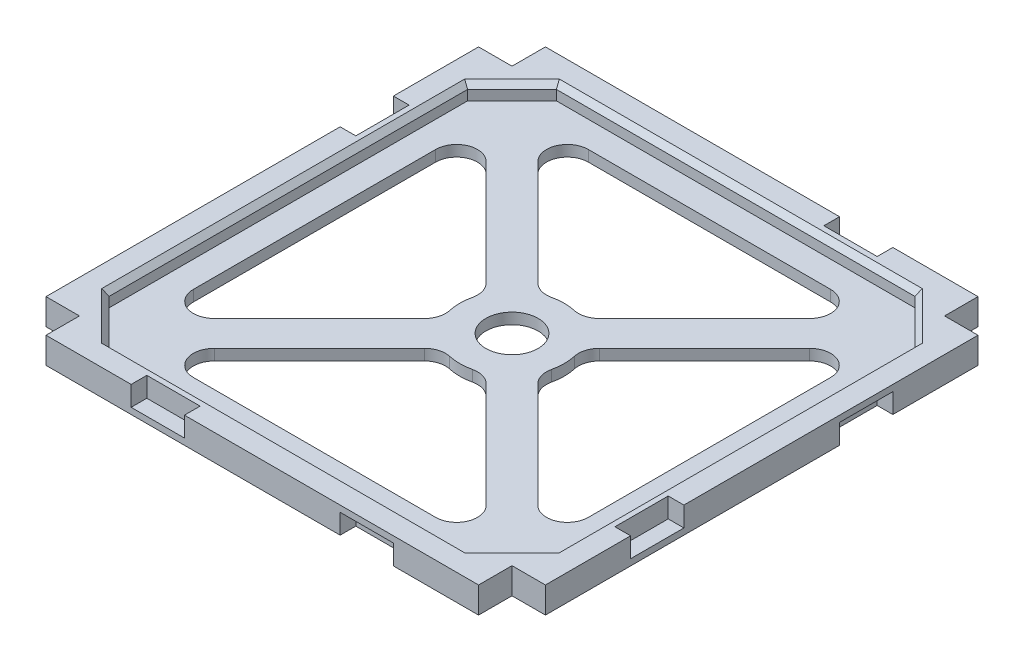
SolidWorks part; units mm, degrees
ref_plane "Front Plane" through (0, 0, 0) normal (0, 0, 1) x (1, 0, 0)
ref_plane "Top Plane" through (0, 0, 0) normal (0, 1, 0) x (1, 0, 0)
ref_plane "Right Plane" through (0, 0, 0) normal (1, 0, 0) x (0, 0, -1)
sketch "Sketch1" plane through (0, 0, 0) normal (0, 1, 0) x (1, 0, 0)
  line L0 (-47.8, -41.4) -> (-47.8, 41.4)
  line L1 (-47.8, 41.4) -> (-41.4, 41.4)
  line L2 (-41.4, 41.4) -> (-41.4, 47.8)
  line L3 (-41.4, 47.8) -> (41.4, 47.8)
  line L4 (41.4, 47.8) -> (41.4, 41.4)
  line L5 (41.4, 41.4) -> (47.8, 41.4)
  line L6 (47.8, 41.4) -> (47.8, -41.4)
  line L7 (47.8, -41.4) -> (41.4, -41.4)
  line L8 (41.4, -41.4) -> (41.4, -47.8)
  line L9 (41.4, -47.8) -> (-41.4, -47.8)
  line L10 (-41.4, -47.8) -> (-41.4, -41.4)
  line L11 (-41.4, -41.4) -> (-47.8, -41.4)
  line L16 (-41.4, 41.4) -> (41.4, -41.4) construction
  line L17 (-41.4, -41.4) -> (41.4, 41.4) construction
  line L18 (-30.9716, -26.0218) -> (-10.834, -5.8843)
  line L19 (-26.0218, -30.9716) -> (-5.8843, -10.834)
  line L20 (26.0218, -30.9716) -> (5.8843, -10.834)
  line L21 (30.9716, -26.0218) -> (10.834, -5.8843)
  line L22 (-26.0218, 30.9716) -> (-5.8843, 10.834)
  line L23 (-30.9716, 26.0218) -> (-10.834, 5.8843)
  line L24 (26.0218, 30.9716) -> (5.8843, 10.834)
  line L25 (10.834, 5.8843) -> (30.9716, 26.0218)
  line L27 (-23.1934, 37.8) -> (23.1934, 37.8)
  line L28 (-37.8, 23.1934) -> (-37.8, -23.1934)
  line L29 (-23.1934, -37.8) -> (23.1934, -37.8)
  line L30 (37.8, 23.1934) -> (37.8, -23.1934)
  line L31 (-37.8, 37.8) -> (37.8, -37.8) construction
  line L32 (-37.8, 37.8) -> (37.8, 37.8) construction
  line L33 (-37.8, 37.8) -> (-37.8, -37.8) construction
  line L34 (-37.8, -37.8) -> (37.8, -37.8) construction
  line L35 (37.8, 37.8) -> (37.8, -37.8) construction
  line L36 (-37.8, 37.8) -> (37.8, -37.8) construction
  line L37 (-37.8, -37.8) -> (37.8, 37.8) construction
  arc A0 (-9.7589, 2.1827) -> (-9.7589, -2.1827) centre (0, 0) ccw
  circle A1 centre (0, 0) radius 5
  arc A2 (2.1827, 9.7589) -> (-2.1827, 9.7589) centre (0, 0) ccw
  arc A3 (-2.1827, -9.7589) -> (2.1827, -9.7589) centre (0, 0) ccw
  arc A4 (9.7589, -2.1827) -> (9.7589, 2.1827) centre (0, 0) ccw
  arc A5 (-23.1934, 37.8) -> (-26.0218, 30.9716) centre (-23.1934, 33.8) ccw
  arc A6 (23.1934, 37.8) -> (26.0218, 30.9716) centre (23.1934, 33.8) cw
  arc A7 (37.8, 23.1934) -> (30.9716, 26.0218) centre (33.8, 23.1934) ccw
  arc A8 (37.8, -23.1934) -> (30.9716, -26.0218) centre (33.8, -23.1934) cw
  arc A9 (26.0218, -30.9716) -> (23.1934, -37.8) centre (23.1934, -33.8) cw
  arc A10 (-23.1934, -37.8) -> (-26.0218, -30.9716) centre (-23.1934, -33.8) cw
  arc A11 (-30.9716, -26.0218) -> (-37.8, -23.1934) centre (-33.8, -23.1934) cw
  arc A12 (-30.9716, 26.0218) -> (-37.8, 23.1934) centre (-33.8, 23.1934) ccw
  arc A13 (-5.8843, 10.834) -> (-2.1827, 9.7589) centre (-3.0558, 13.6624) ccw
  arc A14 (2.1827, 9.7589) -> (5.8843, 10.834) centre (3.0558, 13.6624) ccw
  arc A15 (10.834, 5.8843) -> (9.7589, 2.1827) centre (13.6624, 3.0558) ccw
  arc A16 (9.7589, -2.1827) -> (10.834, -5.8843) centre (13.6624, -3.0558) ccw
  arc A17 (5.8843, -10.834) -> (2.1827, -9.7589) centre (3.0558, -13.6624) ccw
  arc A18 (-2.1827, -9.7589) -> (-5.8843, -10.834) centre (-3.0558, -13.6624) ccw
  arc A19 (-10.834, -5.8843) -> (-9.7589, -2.1827) centre (-13.6624, -3.0558) ccw
  arc A20 (-10.834, 5.8843) -> (-9.7589, 2.1827) centre (-13.6624, 3.0558) cw
  point P14 (0, 0)
  point P19 (0, 0)
  point P37 (0, 0)
  point P58 (4.1489, 9.0987)
  point P63 (9.0987, -4.1489)
  point P66 (4.1489, -9.0987)
  point P69 (-4.1489, -9.0987)
  point P74 (0, 0)
  point P75 (0, 0)
  point P76 (0, 0)
  dimension "D3" = 20
  dimension "D4" = 10
  dimension "D9" = 4
  dimension "D10" = 4
  dimension "D1" = 7
  dimension "D2" = 7
  dimension "D5" = 82.8
  dimension "D6" = 10
  dimension "D7" = 10
  dimension "D8" = 6.4
extrude "Boss-Extrude1" add sketch "Sketch1" along normal blind 2.1 contours L0 L1 L2 L3 L4 L5 L6 L7 L8 L9 L10 L11
sketch "Sketch2" plane through (0, 2.1, 0) normal (0, 1, 0) x (1, 0, 0)
  line L0 (-42.8, 34.3147) -> (-42.8, -34.3147)
  line L1 (-42.8, -34.3147) -> (-34.3147, -42.8)
  line L2 (-34.3147, -42.8) -> (34.3147, -42.8)
  line L3 (34.3147, -42.8) -> (42.8, -34.3147)
  line L4 (42.8, -34.3147) -> (42.8, 34.3147)
  line L5 (42.8, 34.3147) -> (34.3147, 42.8)
  line L6 (34.3147, 42.8) -> (-34.3147, 42.8)
  line L7 (-34.3147, 42.8) -> (-42.8, 34.3147)
  line L12 (-47.8, -41.4) -> (-41.4, -41.4)
  line L13 (-41.4, -41.4) -> (-41.4, -47.8)
  line L14 (-41.4, -47.8) -> (41.4, -47.8)
  line L15 (41.4, -47.8) -> (41.4, -41.4)
  line L16 (41.4, -41.4) -> (47.8, -41.4)
  line L17 (47.8, -41.4) -> (47.8, 41.4)
  line L18 (47.8, 41.4) -> (41.4, 41.4)
  line L19 (41.4, 41.4) -> (41.4, 47.8)
  line L20 (41.4, 47.8) -> (-41.4, 47.8)
  line L21 (-41.4, 47.8) -> (-41.4, 41.4)
  line L22 (-41.4, 41.4) -> (-47.8, 41.4)
  line L23 (-47.8, 41.4) -> (-47.8, -41.4)
  line L24 (-47.8, -41.4) -> (-41.4, -41.4)
  line L25 (-41.4, -41.4) -> (-41.4, -47.8)
  line L26 (-41.4, -47.8) -> (41.4, -47.8)
  line L27 (41.4, -47.8) -> (41.4, -41.4)
  line L28 (41.4, -41.4) -> (47.8, -41.4)
  line L29 (47.8, -41.4) -> (47.8, 41.4)
  line L30 (47.8, 41.4) -> (41.4, 41.4)
  line L31 (41.4, 41.4) -> (41.4, 47.8)
  line L32 (41.4, 47.8) -> (-41.4, 47.8)
  line L33 (-41.4, 47.8) -> (-41.4, 41.4)
  line L34 (-41.4, 41.4) -> (-47.8, 41.4)
  line L35 (-47.8, 41.4) -> (-47.8, -41.4)
  dimension "D2" = 5
  dimension "D3" = 5
  dimension "D4" = 5
  dimension "D5" = 5
  dimension "D6" = 45
  dimension "D7" = 45
  dimension "D8" = 12
extrude "Boss-Extrude2" add sketch "Sketch2" along normal blind 2.9 contours L35 L24 L25 L26 L27 L28 L29 L30 L31 L32 L33 L34
sketch "Sketch3" plane through (-47.8, 0, 0) normal (-1, 0, 0) x (0, 0, 1)
  line L0 (-41.4, 0) -> (41.4, 0) construction
  line L1 (25.1, 0) -> (14.9, 0)
  line L2 (25.1, 0) -> (25.1, 3.8)
  line L3 (25.1, 3.8) -> (14.9, 3.8)
  line L4 (14.9, 0) -> (14.9, 3.8)
  line L5 (25.1, 0) -> (14.9, 3.8) construction
  line L6 (25.1, 3.8) -> (14.9, 0) construction
  line L7 (-41.4, 5) -> (41.4, 5) construction
  line L8 (-25.1, 5) -> (-14.9, 5)
  line L9 (-25.1, 5) -> (-25.1, 1.2)
  line L10 (-25.1, 1.2) -> (-14.9, 1.2)
  line L11 (-14.9, 5) -> (-14.9, 1.2)
  line L12 (-25.1, 5) -> (-14.9, 1.2) construction
  line L13 (-25.1, 1.2) -> (-14.9, 5) construction
  line L14 (-47.8, 2.5) -> (47.8, 2.5) construction
  line L15 (-47.8, 5) -> (-47.8, 0) construction
  line L16 (47.8, 5) -> (47.8, 0) construction
  point P4 (20, 1.9)
  point P11 (-20, 3.1)
  point P20 (-25.1, 3.1)
  point P21 (-14.9, 3.1)
  point P22 (0, 2.5)
  dimension "D2" = 1.3
  dimension "D1" = 1.3
  dimension "D3" = 10.2
  dimension "D4" = 10.2
  dimension "D5" = 29.8
  dimension "D6" = 14.9
extrude "Cut-Extrude1" cut sketch "Sketch3" against normal blind 3
pattern_circular "CirPattern1" count 4 over 360 about axis through (0, 0, 0) along (0, 1, 0) of "Cut-Extrude1"
chamfer "Chamfer1" distance 1 angle 45 8 edges at (38.5574, 5, 38.5574) (42.8, 5, 0) (38.5574, 5, -38.5574) (0, 5, 42.8) (-38.5574, 5, 38.5574) (-42.8, 5, 0) (-38.5574, 5, -38.5574) (0, 5, -42.8)
equation "\"D2@Sketch1\"=\"D1@Sketch1\""
equation "\"D7@Sketch1\"=\"D6@Sketch1\""
equation "\"D9@Sketch1\"=\"D10@Sketch1\""
equation "\"D3@Sketch2\"=\"D2@Sketch2\""
equation "\"D4@Sketch2\"=\"D2@Sketch2\""
equation "\"D5@Sketch2\"=\"D2@Sketch2\""
equation "\"D7@Sketch2\"=\"D6@Sketch2\""
equation "\"D1@Sketch3\"=\"D2@Sketch3\""
equation "\"D4@Sketch3\"=\"D3@Sketch3\""
equation "\"D6@Sketch3\"=\"D5@Sketch3\"/2"
